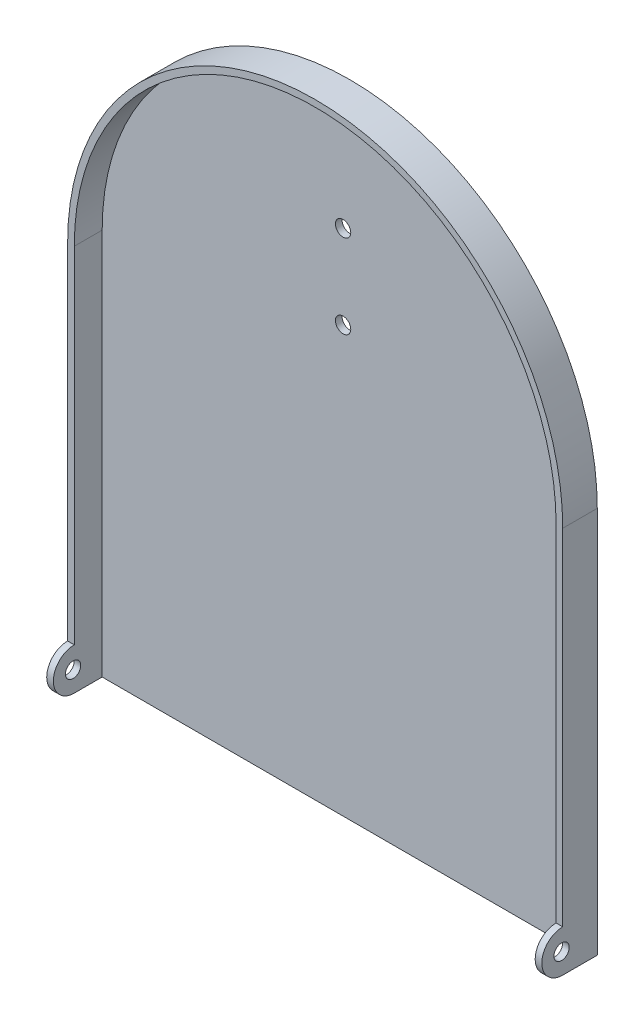
SolidWorks part; units mm, degrees
ref_plane "Front Plane" through (0, 0, 0) normal (0, 0, 1) x (1, 0, 0)
ref_plane "Top Plane" through (0, 0, 0) normal (0, 1, 0) x (1, 0, 0)
ref_plane "Right Plane" through (0, 0, 0) normal (1, 0, 0) x (0, 0, -1)
sketch "Sketch1" plane through (0, 0, 0) normal (0, 0, 1) x (1, 0, 0)
  line L1 (0, 0) -> (177.5, 0)
  line L2 (0, 0) -> (0, 138.75)
  line L3 (0, 138.75) -> (177.5, 138.75) construction
  line L4 (177.5, 0) -> (177.5, 138.75)
  arc A0 (177.5, 138.75) -> (0, 138.75) centre (88.75, 138.75) ccw
  point P6 (88.75, 227.5)
  dimension "D1" = 177.5
  dimension "D2" = 227.5
extrude "Boss-Extrude1" add sketch "Sketch1" along normal blind 2.38 contours L4 A0 L2 L1
sketch "Sketch2" plane through (0, 0, 2.38) normal (0, 0, 1) x (1, 0, 0)
  line L3 (0, 0) -> (0, 138.75) construction
  line L4 (0, 0) -> (177.5, 0) construction
  line L5 (177.5, 0) -> (177.5, 138.75) construction
  line L6 (175.12, 2.38) -> (175.12, 138.75)
  line L7 (2.38, 138.75) -> (2.38, 2.38)
  line L8 (2.38, 2.38) -> (175.12, 2.38)
  line L9 (175.12, 2.38) -> (175.12, 138.75)
  line L10 (2.38, 138.75) -> (2.38, 2.38)
  line L12 (0, 0) -> (0, 138.75)
  line L13 (0, 0) -> (2.38, 0)
  line L14 (177.5, 0) -> (177.5, 138.75)
  line L15 (2.38, 2.38) -> (2.38, 0)
  line L16 (175.12, 2.38) -> (175.12, 0)
  line L17 (175.12, 0) -> (177.5, 0)
  arc A1 (177.5, 138.75) -> (0, 138.75) centre (88.75, 138.75) ccw construction
  arc A2 (175.12, 138.75) -> (2.38, 138.75) centre (88.75, 138.75) ccw
  arc A3 (175.12, 138.75) -> (2.38, 138.75) centre (88.75, 138.75) ccw
  arc A4 (177.5, 138.75) -> (0, 138.75) centre (88.75, 138.75) ccw
  dimension "D1" = 2.38
extrude "Boss-Extrude2" add sketch "Sketch2" along normal blind 10
sketch "Sketch3" plane through (177.5, 0, 0) normal (1, 0, 0) x (0, 0, -1)
  line L0 (-12.38, 0) -> (-12.38, 138.75) construction
  line L1 (-12.38, 15) -> (-12.38, 0)
  arc A0 (-12.38, 15) -> (-12.38, 0) centre (-12.38, 7.5) ccw
  dimension "D1" = 15
extrude "Boss-Extrude3" add sketch "Sketch3" against normal blind 2.38
sketch "Sketch4" plane through (0, 0, 0) normal (-1, 0, 0) x (0, 0, 1)
  line L0 (12.38, 15) -> (12.38, 0)
  arc A0 (12.38, 0) -> (12.38, 15) centre (12.38, 7.5) ccw construction
  arc A1 (12.38, 0) -> (12.38, 15) centre (12.38, 7.5) ccw
extrude "Boss-Extrude4" add sketch "Sketch4" against normal blind 2.38
sketch "Sketch5" plane through (0, 0, 0) normal (-1, 0, 0) x (0, 0, 1)
  circle A0 centre (12.8079, 7.4851) radius 2.75
  dimension "D1" = 5.5
extrude "Cut-Extrude1" cut sketch "Sketch5" against normal through all
sketch "Sketch6" plane through (0, 0, 0) normal (0, 0, -1) x (-1, 0, 0)
  line L0 (-88.75, 227.5) -> (-88.75, 175.9948) construction
  arc A0 (0, 138.75) -> (-177.5, 138.75) centre (-88.75, 138.75) ccw construction
  circle A1 centre (-88.75, 182.5) radius 2.75
  circle A2 centre (-88.75, 152.5) radius 2.75
  dimension "D1" = 5.5
  dimension "D2" = 5.5
  dimension "D3" = 45
  dimension "D4" = 75
extrude "Cut-Extrude2" cut sketch "Sketch6" against normal through all
